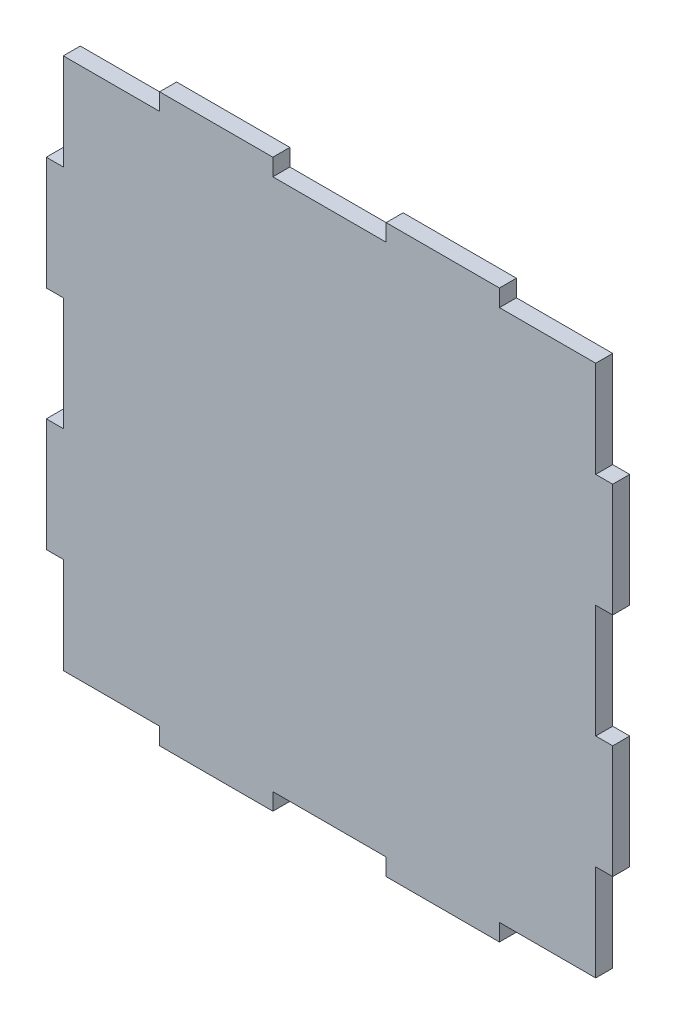
SolidWorks part; units mm, degrees
material "玻璃"
ref_plane "前视基准面" through (0, 0, 0) normal (0, 0, 1) x (1, 0, 0)
ref_plane "上视基准面" through (0, 0, 0) normal (0, 1, 0) x (1, 0, 0)
ref_plane "右视基准面" through (0, 0, 0) normal (1, 0, 0) x (0, 0, -1)
sketch "草图1" plane through (0, 0, 0) normal (0, 0, 1) x (1, 0, 0)
  line L0 (-109.1725, 0) -> (179.0942, 0) construction
  line L1 (0, 126.2991) -> (0, -137.7518) construction
  line L21 (-10, 47) -> (10, 47)
  line L39 (10, 47) -> (10, 50)
  line L40 (10, 50) -> (30, 50)
  line L41 (30, 50) -> (30, 47)
  line L42 (30, 47) -> (47, 47)
  line L43 (0, 0) -> (47, 47) construction
  line L44 (47, 30) -> (47, 47)
  line L45 (50, 30) -> (47, 30)
  line L46 (50, 10) -> (50, 30)
  line L47 (47, 10) -> (50, 10)
  line L48 (47, -10) -> (47, 10)
  line L49 (0, 0) -> (-47, 47) construction
  line L50 (-47, -10) -> (-47, 10)
  line L51 (-47, 10) -> (-50, 10)
  line L52 (-50, 10) -> (-50, 30)
  line L53 (-50, 30) -> (-47, 30)
  line L54 (-47, 30) -> (-47, 47)
  line L55 (-30, 47) -> (-47, 47)
  line L56 (-30, 50) -> (-30, 47)
  line L57 (-10, 50) -> (-30, 50)
  line L58 (-10, 47) -> (-10, 50)
  line L59 (0, 0) -> (-47, -47) construction
  line L61 (-10, -47) -> (-10, -50)
  line L62 (-10, -50) -> (-30, -50)
  line L63 (-30, -50) -> (-30, -47)
  line L64 (-30, -47) -> (-47, -47)
  line L65 (-47, -30) -> (-47, -47)
  line L66 (-50, -30) -> (-47, -30)
  line L67 (-50, -10) -> (-50, -30)
  line L68 (-47, -10) -> (-50, -10)
  line L69 (47, -10) -> (50, -10)
  line L70 (50, -10) -> (50, -30)
  line L71 (50, -30) -> (47, -30)
  line L72 (47, -30) -> (47, -47)
  line L73 (30, -47) -> (47, -47)
  line L74 (30, -50) -> (30, -47)
  line L75 (10, -50) -> (30, -50)
  line L76 (10, -47) -> (10, -50)
  line L77 (-10, -47) -> (10, -47)
  point P26 (0, 47)
  point P36 (-47, 0)
  point P37 (47, 0)
  point P44 (0, -47)
  dimension "D1" = 20
  dimension "D2" = 10
  dimension "D3" = 17
  dimension "D4" = 3
  dimension "D5" = 3
extrude "凸台-拉伸1" add sketch "草图1" along normal blind 3
